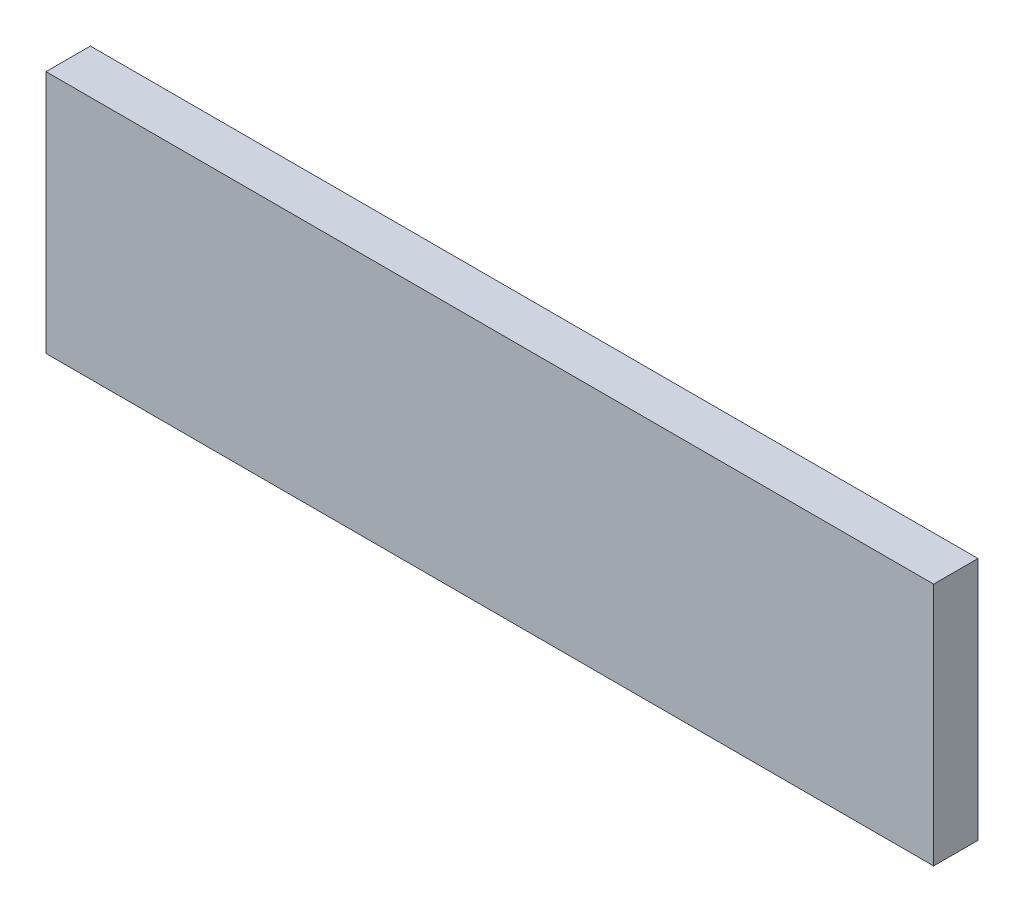
SolidWorks part; units mm, degrees
ref_plane "Front Plane" through (0, 0, 0) normal (0, 0, 1) x (1, 0, 0)
ref_plane "Top Plane" through (0, 0, 0) normal (0, 1, 0) x (1, 0, 0)
ref_plane "Right Plane" through (0, 0, 0) normal (1, 0, 0) x (0, 0, -1)
sketch "Sketch1" plane through (0, 0, 0) normal (0, 0, 1) x (1, 0, 0)
  line L1 (0, 0) -> (-2000, 0)
  line L2 (0, 0) -> (0, -550)
  line L3 (0, -550) -> (-2000, -550)
  line L4 (-2000, 0) -> (-2000, -550)
  dimension "D1" = 550
  dimension "D2" = 2000
extrude "Boss-Extrude1" add sketch "Sketch1" along normal blind 100
